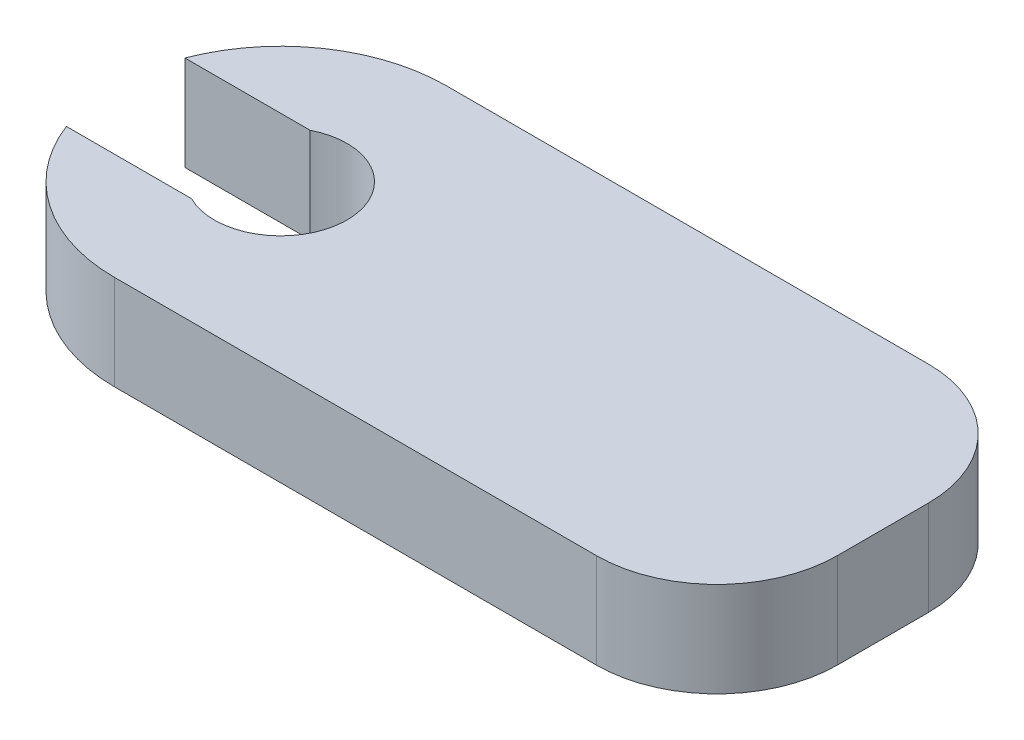
SolidWorks part; units mm, degrees
ref_plane "Front Plane" through (0, 0, 0) normal (0, 0, 1) x (1, 0, 0)
ref_plane "Top Plane" through (0, 0, 0) normal (0, 1, 0) x (1, 0, 0)
ref_plane "Right Plane" through (0, 0, 0) normal (1, 0, 0) x (0, 0, -1)
sketch "Sketch1" plane through (0, 0, 0) normal (0, 1, 0) x (1, 0, 0)
  line L0 (-3.2692, 1.25) -> (-0.6305, 1.25)
  line L1 (-3.2692, -1.25) -> (-0.6305, -1.25)
  line L2 (0, 3.5) -> (10.16, 3.5)
  line L3 (12.7, 0.96) -> (12.7, -0.96)
  line L4 (10.16, -3.5) -> (0, -3.5)
  circle A0 centre (0, 0) radius 1.4
  circle A1 centre (0, 0) radius 3.5
  arc A2 (12.7, -0.96) -> (10.16, -3.5) centre (10.16, -0.96) cw
  arc A3 (10.16, 3.5) -> (12.7, 0.96) centre (10.16, 0.96) cw
  dimension "D1" = 2.8
  dimension "D3" = 7
  dimension "D5" = 2.54
  dimension "D2" = 2.5
  dimension "D4" = 12.7
extrude "Boss-Extrude1" add sketch "Sketch1" along normal blind 2 contours L1 A1 L0 A0 | A1 L4 L3 L2
